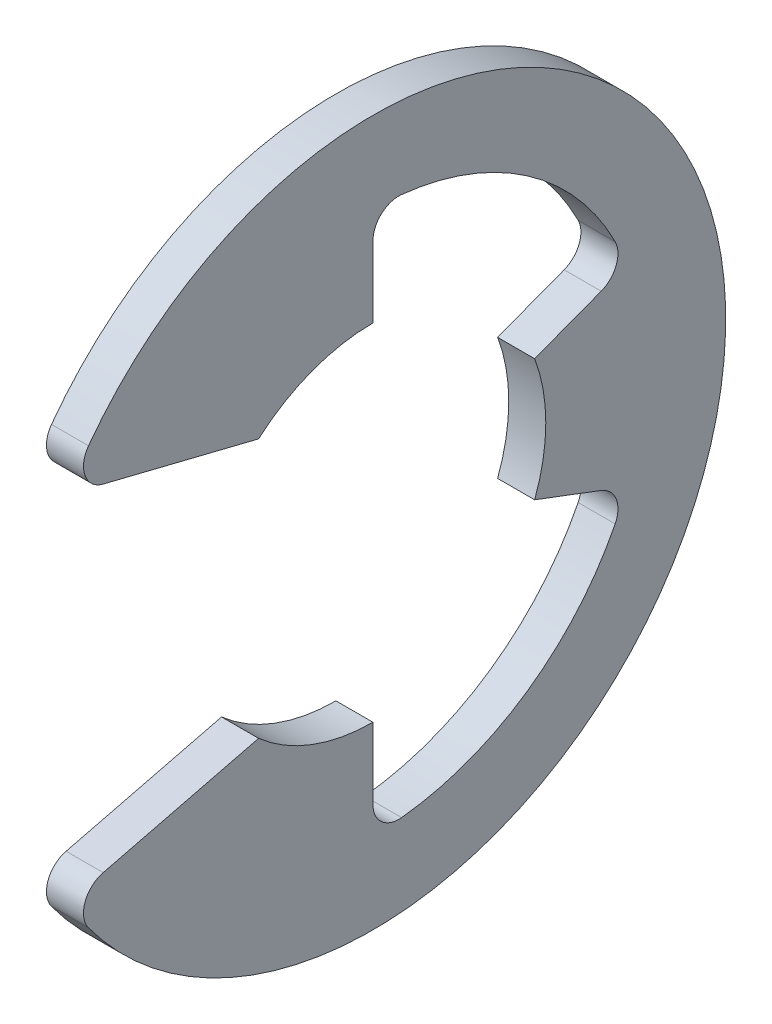
SolidWorks part; units mm, degrees
material "AISI 1020"
ref_plane "Front" through (0, 0, 0) normal (0, 0, 1) x (1, 0, 0)
ref_plane "Top" through (0, 0, 0) normal (0, 1, 0) x (1, 0, 0)
ref_plane "Right" through (0, 0, 0) normal (1, 0, 0) x (0, 0, -1)
sketch "Sketch1" plane through (0, 0, 0) normal (1, 0, 0) x (0, 0, -1)
  line L0 (-8.7883, -5.0981) -> (-3.2929, -3.7338)
  line L1 (-8.7883, 5.0981) -> (-3.2929, 3.7338)
  line L2 (0, -4.9784) -> (0, -7.8134)
  line L3 (0, 4.9784) -> (0, 7.8134)
  line L4 (4.6569, -1.7601) -> (7.3087, -2.7624)
  line L5 (4.6569, 1.7601) -> (7.3087, 2.7624)
  line L6 (0, 0) -> (-10.414, 0) construction
  line L7 (4.6569, 1.7601) -> (4.6569, -1.7601) construction
  line L8 (0, -4.9784) -> (-3.2929, -3.7338) construction
  line L9 (0, 10.16) -> (0, -10.16) construction
  circle A1 centre (0, 0) radius 10.414 construction
  circle A2 centre (0, 0) radius 4.9784 construction
  arc A3 (-8.7883, -5.0981) -> (-8.7883, 5.0981) centre (0, 0) ccw
  arc A4 (-3.2929, -3.7338) -> (0, -4.9784) centre (0, 0) ccw
  arc A5 (-3.2929, 3.7338) -> (0, 4.9784) centre (0, 0) cw
  arc A6 (4.6569, 1.7601) -> (4.6569, -1.7601) centre (0, 0) cw
  arc A7 (0, -7.8134) -> (7.3087, -2.7624) centre (0, 0) ccw
  arc A8 (7.3087, 2.7624) -> (0, 7.8134) centre (0, 0) ccw
  dimension "D1" = 7.8134
  dimension "OD" = 20.32
  dimension "L" = 20.828
  dimension "D" = 9.9568
  dimension "D2" = 5.6607
  dimension "D3" = 7.4676
extrude "Extrude1" add sketch "Sketch1" along normal mid plane 1.0668
fillet "Fillet1" radius 0.7468 6 edges at (0, -7.8134, 0) (0, 7.8134, 0) (0, -5.0981, 8.7883) (0, 5.0981, 8.7883) (0, -2.7624, -7.3087) (0, 2.7624, -7.3087)
sketch "Sketch3" plane through (0, 0, 0) normal (0, 1, 0) x (1, 0, 0)
  line L0 (0.5842, 6.35) -> (0.5842, 5.0292)
  line L1 (0.5842, 5.0292) -> (-0.5842, 5.0292)
  line L2 (-0.5842, 5.0292) -> (-0.5842, 6.35)
  line L3 (-0.5842, 6.35) -> (-12.5603, 6.35)
  line L4 (4.9657, 0) -> (4.9657, 5.6896)
  line L5 (-12.5603, 6.35) -> (-12.5603, 0)
  line L6 (-12.5603, 0) -> (4.9657, 0)
  line L8 (4.9657, 0) -> (4.9657, 6.35) construction
  line L9 (4.9657, 6.35) -> (0.5842, 6.35) construction
  line L10 (4.9657, 0) -> (17.2631, 0) construction
  line L11 (4.9657, 5.6896) -> (4.3053, 6.35)
  line L12 (4.3053, 6.35) -> (0.5842, 6.35)
  point P2 (0, 5.0292)
  point P5 (0.5842, 5.6896)
  dimension "D1" = 4.3815
  dimension "Ds" = 12.7
  dimension "Dg" = 10.0584
  dimension "W" = 1.1684
  dimension "D2" = 17.526
  dimension "D3" = 45
revolve "Revolve2" [suppressed] add sketch "Sketch3" angle 360 about L10
equation "\"D2@Sketch3\" = \"W@Sketch3\"*15"
equation "\"D1@Sketch3\" = \"D2@Sketch3\"/4"
equation "\"D1@Sketch1\" = (\"OD@Sketch1\"+\"D@Sketch1\")/3.875"
equation "\"D3@Sketch1\" = \"D@Sketch1\"*.75"
equation "\"D1@Fillet1\" = \"D1@Extrude1\"*.7"
